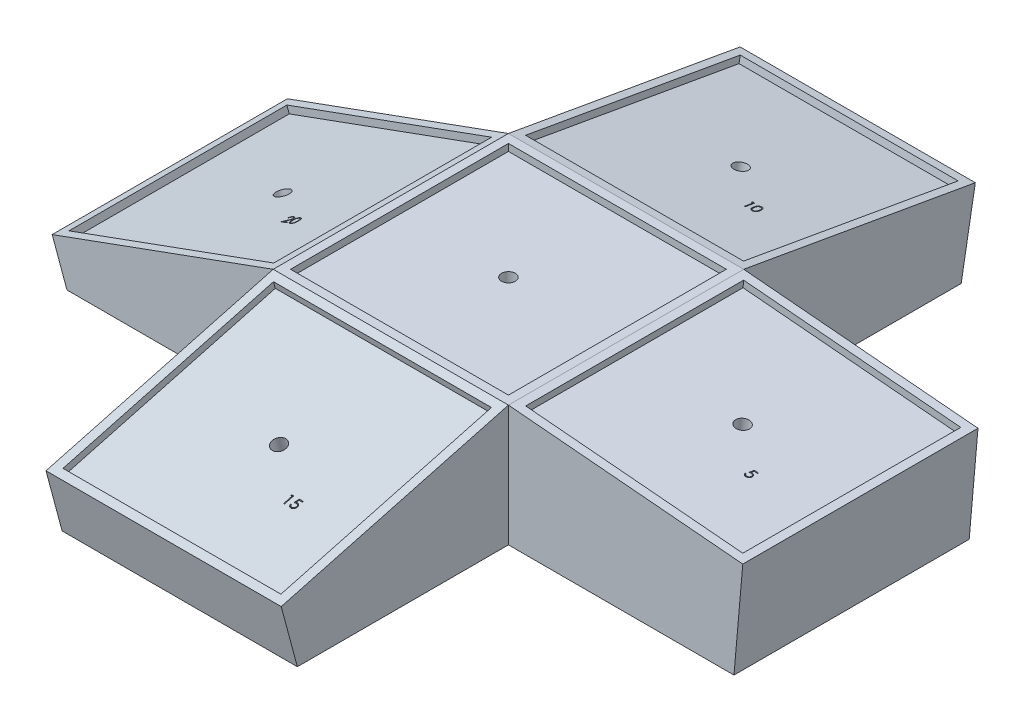
SolidWorks part; units mm, degrees
ref_plane "Front Plane" through (0, 0, 0) normal (0, 0, 1) x (1, 0, 0)
ref_plane "Top Plane" through (0, 0, 0) normal (0, 1, 0) x (1, 0, 0)
ref_plane "Right Plane" through (0, 0, 0) normal (1, 0, 0) x (0, 0, -1)
sketch "Sketch1" plane through (0, 0, 0) normal (0, 1, 0) x (1, 0, 0)
  line L1 (0, 0) -> (80.01, 0)
  line L2 (0, 0) -> (0, 80.01)
  line L3 (0, 80.01) -> (80.01, 80.01)
  line L4 (80.01, 0) -> (80.01, 80.01)
  line L5 (-3.175, 83.185) -> (83.185, 83.185)
  line L6 (-3.175, 83.185) -> (-3.175, -3.175)
  line L7 (-3.175, -3.175) -> (83.185, -3.175)
  line L8 (83.185, 83.185) -> (83.185, -3.175)
  dimension "D1" = 80.01
  dimension "D2" = 80.01
  dimension "D3" = 3.175
  dimension "D4" = 3.175
  dimension "D5" = 3.175
  dimension "D6" = 3.175
extrude "Boss-Extrude1" add sketch "Sketch1" along normal blind 2.54
sketch "Sketch2" plane through (0, 0, 0) normal (0, -1, 0) x (1, 0, 0)
  line L1 (-3.175, 3.175) -> (83.185, 3.175)
  line L2 (-3.175, 3.175) -> (-3.175, -83.185)
  line L3 (-3.175, -83.185) -> (83.185, -83.185)
  line L4 (83.185, 3.175) -> (83.185, -83.185)
  line L6 (-3.175, 3.175) -> (83.185, 3.175) construction
  line L7 (-3.175, -83.185) -> (-3.175, 3.175) construction
  line L8 (83.185, -83.185) -> (-3.175, -83.185) construction
  point P4 (0, -3.638)
  point P5 (0, 0)
  point P8 (8.7084, -85.725)
  point P11 (21.3702, -57.5989)
extrude "Boss-Extrude2" add sketch "Sketch2" along normal blind 8.89
sketch "Sketch3" plane through (0, 0, 0) normal (0, 1, 0) x (1, 0, 0)
  line L1 (-3.175, -3.175) -> (83.185, -3.175) construction
  line L2 (83.185, -3.175) -> (83.185, 83.185) construction
  circle A0 centre (40.005, 40.005) radius 2.54
  dimension "D1" = 5.08
  dimension "D2" = 43.18
  dimension "D3" = 43.18
extrude "Cut-Extrude1" cut sketch "Sketch3" against normal blind 8.89
ref_plane "Plane1" through (0.8524, 9.7432, 0) normal (0.0872, 0.9962, 0) x (0, 0, -1)
sketch "Sketch4" plane through (0.8524, 9.7432, 0) normal (0.0872, 0.9962, 0) x (0, 0, -1)
  line L1 (-3.175, -82.6471) -> (83.185, -82.6471)
  line L2 (-3.175, -82.6471) -> (-3.175, -169.0071)
  line L3 (-3.175, -169.0071) -> (83.185, -169.0071)
  line L4 (83.185, -82.6471) -> (83.185, -169.0071)
  line L6 (0, -85.8221) -> (80.01, -85.8221)
  line L7 (0, -85.8221) -> (0, -165.8321)
  line L8 (0, -165.8321) -> (80.01, -165.8321)
  line L9 (80.01, -85.8221) -> (80.01, -165.8321)
  line L12 (-3.175, -82.6471) -> (83.185, -82.6471) construction
  line L13 (83.185, -82.6471) -> (83.185, 3.3843) construction
  dimension "D1" = 86.36
  dimension "D2" = 86.36
  dimension "D3" = 80.01
  dimension "D4" = 80.01
  dimension "D5" = 3.175
  dimension "D6" = 3.175
extrude "Boss-Extrude3" add sketch "Sketch4" against normal blind 2.54 separate body
sketch "Sketch5" plane through (0.631, 7.2128, 0) normal (-0.0872, -0.9962, 0) x (0.9962, -0.0872, 0)
  line L0 (82.6471, 3.175) -> (169.0071, 3.175) construction
  line L1 (82.6471, 3.175) -> (169.0071, 3.175)
  line L2 (82.6471, 3.175) -> (82.6471, -83.185)
  line L3 (82.6471, -83.185) -> (169.0071, -83.185)
  line L4 (169.0071, 3.175) -> (169.0071, -83.185)
  dimension "D1" = 86.36
extrude "Boss-Extrude4" add sketch "Sketch5" along normal blind 8.89
sketch "Sketch6" plane through (0.631, 7.2128, 0) normal (0.0872, 0.9962, 0) x (0.9962, -0.0872, 0)
  line L0 (169.0071, -3.175) -> (169.0071, 83.185) construction
  line L1 (82.6471, -3.175) -> (169.0071, -3.175) construction
  circle A0 centre (125.8271, 40.005) radius 2.54
  dimension "D1" = 43.18
  dimension "D3" = 5.08
  dimension "D2" = 43.18
extrude "Cut-Extrude2" cut sketch "Sketch6" against normal blind 8.89
ref_plane "Plane2" through (0, 16.6889, -2.9427) normal (0, 0.9848, -0.1736) x (-1, 0, 0)
sketch "Sketch7" plane through (0, 16.6889, -2.9427) normal (0, 0.9848, -0.1736) x (-1, 0, 0)
  line L1 (-83.185, -81.4802) -> (3.175, -81.4802)
  line L2 (-83.185, -81.4802) -> (-83.185, -167.8402)
  line L3 (-83.185, -167.8402) -> (3.175, -167.8402)
  line L4 (3.175, -81.4802) -> (3.175, -167.8402)
  line L5 (-80.01, -84.6552) -> (0, -84.6552)
  line L6 (-80.01, -84.6552) -> (-80.01, -164.6652)
  line L7 (-80.01, -164.6652) -> (0, -164.6652)
  line L8 (0, -84.6552) -> (0, -164.6652)
  dimension "D1" = 86.36
  dimension "D2" = 86.36
  dimension "D3" = 80.01
  dimension "D4" = 80.01
  dimension "D5" = 3.175
  dimension "D6" = 3.175
extrude "Boss-Extrude5" add sketch "Sketch7" against normal blind 2.54
sketch "Sketch8" plane through (0, 14.1875, -2.5016) normal (0, -0.9848, 0.1736) x (1, 0, 0)
  line L6 (-3.175, -81.4802) -> (83.185, -81.4802)
  line L7 (-3.175, -81.4802) -> (-3.175, -167.8402)
  line L8 (-3.175, -167.8402) -> (83.185, -167.8402)
  line L9 (83.185, -81.4802) -> (83.185, -167.8402)
  dimension "D1" = 86.36
  dimension "D2" = 86.36
extrude "Boss-Extrude6" add sketch "Sketch8" along normal blind 8.89
sketch "Sketch9" plane through (0, 14.1875, -2.5016) normal (0, 0.9848, -0.1736) x (1, 0, 0)
  line L0 (83.185, 81.4802) -> (-3.175, 81.4802) construction
  line L1 (-3.175, 167.8402) -> (-3.175, 81.4802) construction
  circle A0 centre (40.005, 124.6602) radius 2.54
  dimension "D1" = 43.18
  dimension "D3" = 5.08
  dimension "D2" = 43.18
extrude "Cut-Extrude3" cut sketch "Sketch9" against normal blind 8.89
ref_plane "Plane3" through (0, 3.1636, 0.8477) normal (0, 0.9659, 0.2588) x (1, 0, 0)
sketch "Sketch10" plane through (0, 3.1636, 0.8477) normal (0, 0.9659, 0.2588) x (1, 0, 0)
  line L1 (-3.175, -2.4094) -> (83.185, -2.4094)
  line L2 (-3.175, -2.4094) -> (-3.175, -88.7694)
  line L3 (-3.175, -88.7694) -> (83.185, -88.7694)
  line L4 (83.185, -2.4094) -> (83.185, -88.7694)
  line L5 (0, -5.5844) -> (80.01, -5.5844)
  line L6 (0, -5.5844) -> (0, -85.5944)
  line L7 (0, -85.5944) -> (80.01, -85.5944)
  line L8 (80.01, -5.5844) -> (80.01, -85.5944)
  dimension "D1" = 86.36
  dimension "D2" = 86.36
  dimension "D3" = 80.01
  dimension "D4" = 80.01
  dimension "D5" = 3.175
  dimension "D6" = 3.175
extrude "Boss-Extrude7" add sketch "Sketch10" against normal blind 2.54
sketch "Sketch11" plane through (0, 0.7102, 0.1903) normal (0, -0.9659, -0.2588) x (1, 0, 0)
  line L0 (83.185, 88.7694) -> (83.185, 3.09) construction
  line L1 (-3.175, 88.7694) -> (83.185, 88.7694)
  line L2 (-3.175, 88.7694) -> (-3.175, 2.4094)
  line L3 (-3.175, 2.4094) -> (83.185, 2.4094)
  line L4 (83.185, 88.7694) -> (83.185, 2.4094)
  dimension "D1" = 86.36
extrude "Boss-Extrude8" add sketch "Sketch11" along normal blind 8.89
sketch "Sketch12" plane through (0, 0.7102, 0.1903) normal (0, 0.9659, 0.2588) x (1, 0, 0)
  line L0 (-3.175, -2.4094) -> (83.185, -2.4094) construction
  line L1 (-3.175, -2.4094) -> (-3.175, -88.7694) construction
  circle A0 centre (40.005, -45.5894) radius 2.54
  dimension "D1" = 43.18
  dimension "D3" = 5.08
  dimension "D2" = 43.18
extrude "Cut-Extrude4" cut sketch "Sketch12" against normal blind 8.89
ref_plane "Plane4" through (-1.1877, 3.2633, 0) normal (-0.342, 0.9397, 0) x (0, 0, 1)
sketch "Sketch14" plane through (-1.1877, 3.2633, 0) normal (-0.342, 0.9397, 0) x (0, 0, 1)
  line L1 (-83.185, -2.1148) -> (3.175, -2.1148)
  line L2 (-83.185, -2.1148) -> (-83.185, -88.4748)
  line L3 (-83.185, -88.4748) -> (3.175, -88.4748)
  line L4 (3.175, -2.1148) -> (3.175, -88.4748)
  line L5 (-80.01, -5.2898) -> (0, -5.2898)
  line L6 (-80.01, -5.2898) -> (-80.01, -85.2998)
  line L7 (-80.01, -85.2998) -> (0, -85.2998)
  line L8 (0, -5.2898) -> (0, -85.2998)
  point P9 (0, 0)
  dimension "D1" = 86.36
  dimension "D2" = 86.36
  dimension "D3" = 80.01
  dimension "D4" = 80.01
  dimension "D5" = 3.175
  dimension "D6" = 3.175
extrude "Boss-Extrude10" add sketch "Sketch14" against normal blind 2.54
sketch "Sketch15" plane through (-0.319, 0.8765, 0) normal (0.342, -0.9397, 0) x (0, 0, -1)
  line L0 (83.185, -3.0393) -> (83.185, -88.4748) construction
  line L1 (-3.175, -88.4748) -> (83.185, -88.4748)
  line L2 (-3.175, -88.4748) -> (-3.175, -2.1148)
  line L3 (-3.175, -2.1148) -> (83.185, -2.1148)
  line L4 (83.185, -88.4748) -> (83.185, -2.1148)
  dimension "D1" = 86.36
extrude "Boss-Extrude11" add sketch "Sketch15" along normal blind 8.89
sketch "Sketch16" plane through (-0.319, 0.8765, 0) normal (-0.342, 0.9397, 0) x (0, 0, 1)
  line L0 (-83.185, -88.4748) -> (3.175, -88.4748) construction
  line L1 (-83.185, -2.1148) -> (-83.185, -88.4748) construction
  circle A0 centre (-40.005, -45.2948) radius 2.54
  dimension "D1" = 43.18
  dimension "D3" = 5.08
  dimension "D2" = 43.18
extrude "Cut-Extrude5" cut sketch "Sketch16" against normal blind 8.89
ref_plane "Plane5" through (0, -41.91, 0) normal (0, 1, 0) x (1, 0, 0)
sketch "Sketch29" plane through (0.631, 7.2128, 0) normal (0.0872, 0.9962, 0) x (0.9962, -0.0872, 0)
  line L0 (165.8321, 0) -> (165.8321, 80.01) construction
  line L1 (85.8221, 0) -> (165.8321, 0) construction
  text T0 "5"
  point P1 (75.3438, 27.5232)
  dimension "D1" = 25.4
  dimension "D2" = 25.4
extrude "Cut-Extrude11" cut sketch "Sketch29" against normal blind 2.54
sketch "Sketch30" plane through (0, 14.1875, -2.5016) normal (0, 0.9848, -0.1736) x (1, 0, 0)
  line L0 (80.01, 84.6552) -> (80.01, 164.6652) construction
  line L1 (0, 84.6552) -> (80.01, 84.6552) construction
  text T0 "10"
  point P1 (0, 0)
  point P2 (11.1271, 89.3425)
  point P3 (46.7124, 113.4064)
  point P8 (56.4648, 113.4813)
  dimension "D1" = 25.4
  dimension "D2" = 25.4
extrude "Cut-Extrude12" cut sketch "Sketch30" against normal blind 2.54
sketch "Sketch31" plane through (0, 0.7102, 0.1903) normal (0, 0.9659, 0.2588) x (1, 0, 0)
  line L0 (80.01, -85.5944) -> (80.01, -5.5844) construction
  line L1 (0, -85.5944) -> (80.01, -85.5944) construction
  text T0 "15"
  point P1 (60.114, -72.7218)
  dimension "D1" = 25.4
  dimension "D2" = 25.4
extrude "Cut-Extrude13" cut sketch "Sketch31" against normal blind 2.54
sketch "Sketch32" plane through (-0.319, 0.8765, 0) normal (-0.342, 0.9397, 0) x (0.9397, 0.342, 0)
  line L0 (-5.2898, 0) -> (-5.2898, 80.01) construction
  line L1 (-85.2998, 0) -> (-5.2898, 0) construction
  text T0 "20"
  point P1 (-50.2083, 24.0185)
  point P2 (-50.2083, 28.3617)
  dimension "D1" = 25.4
  dimension "D2" = 25.4
extrude "Cut-Extrude14" cut sketch "Sketch32" against normal blind 2.54
sketch "Sketch35" plane through (0, -41.91, 0) normal (0, 1, 0) x (1, 0, 0)
  line L1 (-84.3269, 83.185) -> (-3.175, 83.185)
  line L2 (-84.3269, 83.185) -> (-84.3269, -3.175)
  line L3 (-84.3269, -3.175) -> (-3.175, -3.175)
  line L4 (-3.175, 83.185) -> (-3.175, -3.175)
extrude "Boss-Extrude12" add sketch "Sketch35" along normal up to surface (32.2864 mm away)
sketch "Sketch36" plane through (2.7215, -7.4774, 0) normal (-0.342, 0.9397, 0) x (0.9397, 0.342, 0)
  line L0 (-93.5754, 83.185) -> (-93.5754, -3.175) construction
  line L1 (-93.5754, 85.725) -> (-88.4748, 85.725)
  line L2 (-93.5754, 85.725) -> (-93.5754, -3.175)
  line L3 (-93.5754, -3.175) -> (-88.4748, -3.175)
  line L4 (-88.4748, 85.725) -> (-88.4748, -3.175)
extrude "Cut-Extrude15" cut sketch "Sketch36" against normal up to surface (4.4402 mm away)
sketch "Sketch40" plane through (0, -41.91, 0) normal (0, 1, 0) x (1, 0, 0)
  line L1 (-3.175, 83.185) -> (83.185, 83.185)
  line L2 (-3.175, 83.185) -> (-3.175, -3.175)
  line L3 (-3.175, -3.175) -> (83.185, -3.175)
  line L4 (83.185, 83.185) -> (83.185, -3.175)
extrude "Boss-Extrude16" add sketch "Sketch40" along normal up to surface (33.02 mm away) up to face at (40.005, -8.89, -37.465)
sketch "Sketch41" plane through (0, -41.91, 0) normal (0, 1, 0) x (1, 0, 0)
  line L1 (-3.175, -3.175) -> (83.185, -3.175)
  line L2 (-3.175, -3.175) -> (-3.175, -86.5924)
  line L3 (-3.175, -86.5924) -> (83.185, -86.5924)
  line L4 (83.185, -3.175) -> (83.185, -86.5924)
extrude "Boss-Extrude17" add sketch "Sketch41" along normal up to surface (32.6168 mm away)
sketch "Sketch42" plane through (0, -7.8769, -2.1106) normal (0, 0.9659, 0.2588) x (1, 0, 0)
  line L0 (83.185, -88.7694) -> (83.185, -91.8321) construction
  line L1 (-3.175, -88.7694) -> (83.185, -88.7694)
  line L2 (-3.175, -88.7694) -> (-3.175, -94.4889)
  line L3 (-3.175, -94.4889) -> (83.185, -94.4889)
  line L4 (83.185, -88.7694) -> (83.185, -94.4889)
  line L5 (-3.175, -94.4889) -> (83.185, -94.4889) construction
extrude "Cut-Extrude16" cut sketch "Sketch42" against normal up to surface (11.4479 mm away)
sketch "Sketch43" plane through (0, -41.91, 0) normal (0, 1, 0) x (1, 0, 0)
  line L1 (83.185, 83.185) -> (169.2164, 83.185)
  line L2 (83.185, 83.185) -> (83.185, -3.175)
  line L3 (83.185, -3.175) -> (169.2164, -3.175)
  line L4 (169.2164, 83.185) -> (169.2164, -3.175)
extrude "Boss-Extrude18" add sketch "Sketch43" along normal up to surface (25.4496 mm away)
sketch "Sketch44" plane through (-0.1438, -1.6433, 0) normal (0.0872, 0.9962, 0) x (0.9962, -0.0872, 0)
  line L0 (170.0071, -3.175) -> (169.0071, -3.175) construction
  line L1 (169.0071, 83.185) -> (172.2252, 83.185)
  line L2 (169.0071, 83.185) -> (169.0071, -3.175)
  line L3 (169.0071, -3.175) -> (172.2252, -3.175)
  line L4 (172.2252, 83.185) -> (172.2252, -3.175)
  line L5 (172.2252, -3.175) -> (172.2252, 83.185) construction
extrude "Cut-Extrude19" cut sketch "Sketch44" against normal up to surface (25.3527 mm away)
sketch "Sketch45" plane through (0, -41.91, 0) normal (0, 1, 0) x (1, 0, 0)
  line L1 (-3.175, 168.233) -> (83.185, 168.233)
  line L2 (-3.175, 168.233) -> (-3.175, 83.185)
  line L3 (-3.175, 83.185) -> (83.185, 83.185)
  line L4 (83.185, 168.233) -> (83.185, 83.185)
extrude "Boss-Extrude19" add sketch "Sketch45" along normal up to surface (17.8474 mm away)
sketch "Sketch46" plane through (0, 5.4325, -0.9579) normal (0, 0.9848, -0.1736) x (1, 0, 0)
  line L0 (83.185, 169.8556) -> (83.185, 167.8402) construction
  line L1 (-3.175, 167.8402) -> (83.185, 167.8402)
  line L2 (-3.175, 167.8402) -> (-3.175, 172.9548)
  line L3 (-3.175, 172.9548) -> (83.185, 172.9548)
  line L4 (83.185, 167.8402) -> (83.185, 172.9548)
  line L5 (83.185, 172.9548) -> (-3.175, 172.9548) construction
extrude "Cut-Extrude20" cut sketch "Sketch46" against normal up to surface (18.4781 mm away)
